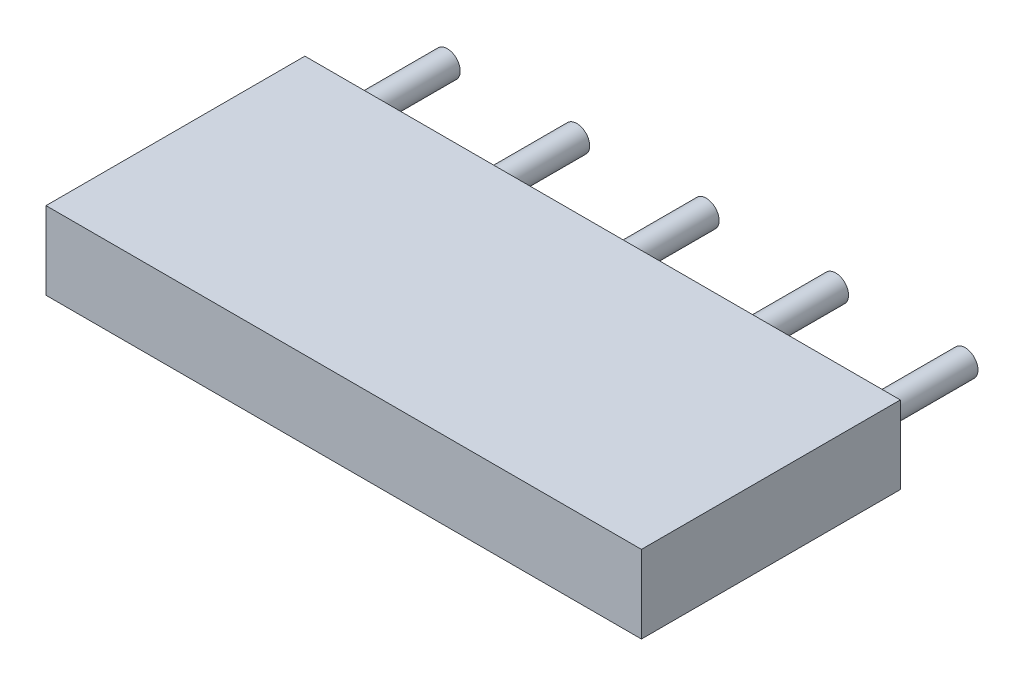
SolidWorks part; units mm, degrees
ref_plane "Front Plane" through (0, 0, 0) normal (0, 0, 1) x (1, 0, 0)
ref_plane "Top Plane" through (0, 0, 0) normal (0, 1, 0) x (1, 0, 0)
ref_plane "Right Plane" through (0, 0, 0) normal (1, 0, 0) x (0, 0, -1)
sketch "Sketch1" plane through (0, 0, 0) normal (0, 0, 1) x (1, 0, 0)
  line L0 (-0.75, 0.75) -> (-0.75, -0.75)
  line L1 (-0.75, -0.75) -> (10.75, -0.75)
  line L2 (10.75, -0.75) -> (10.75, 0.75)
  line L3 (10.75, 0.75) -> (-0.75, 0.75)
extrude "Component_Outline" add sketch "Sketch1" along normal blind 5 separate body
sketch "Sketch2" plane through (0, 0, 0) normal (0, 0, 1) x (1, 0, 0)
  circle A0 centre (0, 0) radius 0.25
extrude "1" add sketch "Sketch2" against normal blind 2 separate body
sketch "Sketch3" plane through (0, 0, 0) normal (0, 0, 1) x (1, 0, 0)
  circle A0 centre (2.5, 0) radius 0.25
extrude "2" add sketch "Sketch3" against normal blind 2 separate body
sketch "Sketch4" plane through (0, 0, 0) normal (0, 0, 1) x (1, 0, 0)
  circle A0 centre (5, 0) radius 0.25
extrude "3" add sketch "Sketch4" against normal blind 2 separate body
sketch "Sketch5" plane through (0, 0, 0) normal (0, 0, 1) x (1, 0, 0)
  circle A0 centre (7.5, 0) radius 0.25
extrude "4" add sketch "Sketch5" against normal blind 2 separate body
sketch "Sketch6" plane through (0, 0, 0) normal (0, 0, 1) x (1, 0, 0)
  circle A0 centre (10, 0) radius 0.25
extrude "5" add sketch "Sketch6" against normal blind 2 separate body
sketch3d "3DSketch1"
  line L0 (0, 0, 0) -> (1, 0, 0)
  line L1 (0, 0, 0) -> (0, 1, 0)
  line L2 (0, 0, 0) -> (0, 0, 1)
  point P0 (0, 0, 0)
